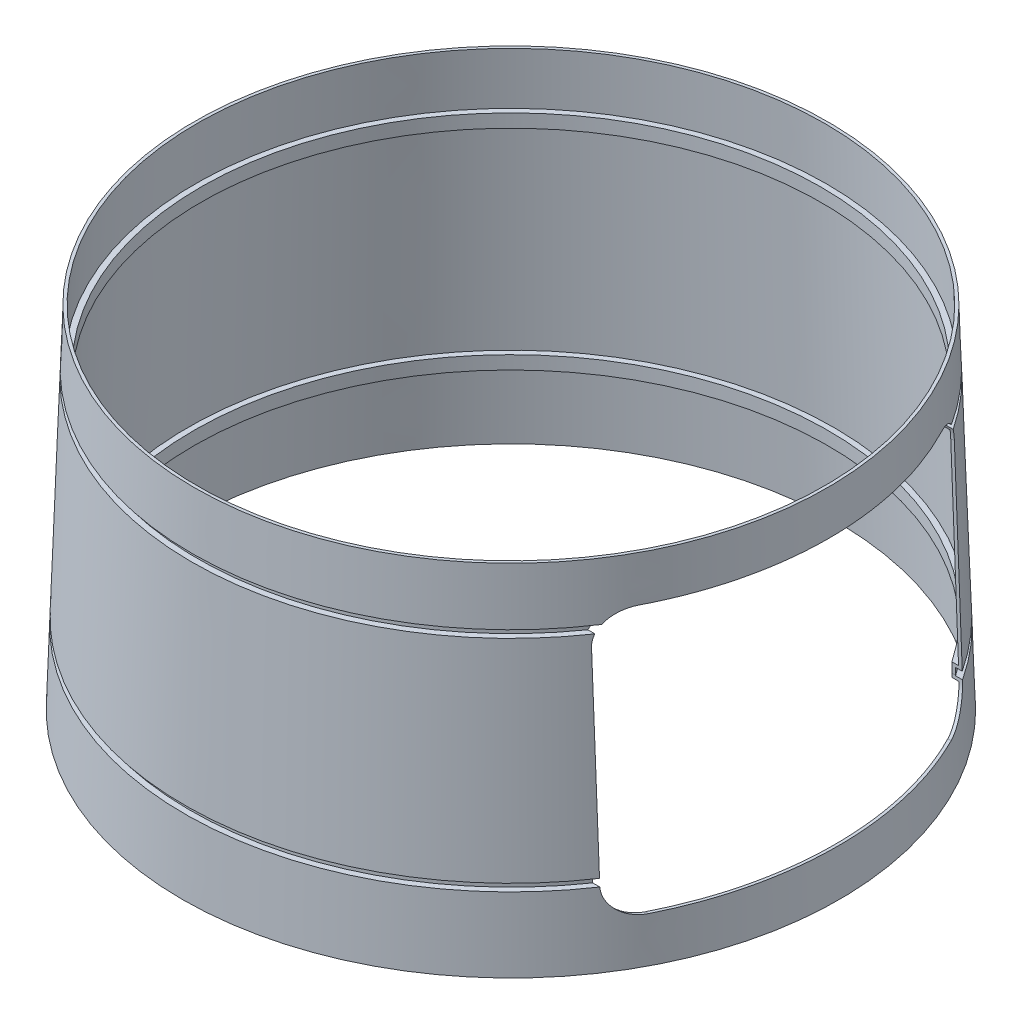
SolidWorks part; units mm, degrees
ref_plane "Front" through (0, 0, 0) normal (0, 0, 1) x (1, 0, 0)
ref_plane "Top" through (0, 0, 0) normal (0, 1, 0) x (1, 0, 0)
ref_plane "Right" through (0, 0, 0) normal (1, 0, 0) x (0, 0, -1)
sketch "Sketch1" plane through (0, 0, 0) normal (0, 0, 1) x (1, 0, 0)
  line L0 (0, 0) -> (109.9792, 0)
  line L1 (109.9792, 0) -> (109.1612, 24.3759)
  line L2 (106.0385, 117.4292) -> (0, 117.4292)
  line L3 (0, 117.4292) -> (0, 0)
  line L4 (106.6704, 98.5997) -> (104.8, 98.5997)
  line L5 (104.8, 98.5997) -> (104.8, 96.1587)
  line L6 (104.8, 96.1587) -> (106.7523, 96.1587)
  line L7 (109.0793, 26.8169) -> (107.2089, 26.8169)
  line L8 (107.2089, 26.8169) -> (107.2089, 24.3759)
  line L9 (107.2089, 24.3759) -> (109.1612, 24.3759)
  line L10 (106.6704, 98.5997) -> (106.0385, 117.4292)
  line L11 (109.0793, 26.8169) -> (106.7523, 96.1587)
  line L12 (109.9792, 0) -> (-109.9792, 0) construction
  dimension "D1" = 88.078
revolve "Revolve1" add sketch "Sketch1" angle 360 about L3
shell "Shell1" thickness 1
ref_plane "Plane1" through (109.8555, 3.6865, 0) normal (0.9994, 0.0335, 0) x (0, 0, -1)
sketch "Sketch2" plane through (109.8555, 3.6865, 0) normal (0.9994, 0.0335, 0) x (0, 0, -1)
  line L1 (-50.8692, 11.5651) -> (49.8692, 11.5651)
  line L2 (-60.8692, 21.5651) -> (-60.8692, 89.3601)
  line L3 (-50.8692, 99.3601) -> (49.8692, 99.3601)
  line L4 (59.8692, 21.5651) -> (59.8692, 89.3601)
  line L5 (-60.8692, 11.5651) -> (59.8692, 99.3601) construction
  line L6 (-60.8692, 99.3601) -> (59.8692, 11.5651) construction
  line L12 (54.3692, 99.3601) -> (-54.3692, 99.3601) construction
  line L13 (59.8692, 8.2741) -> (59.8692, 93.8632) construction
  arc A0 (49.8692, 99.3601) -> (59.8692, 89.3601) centre (49.8692, 89.3601) cw
  arc A1 (-50.8692, 11.5651) -> (-60.8692, 21.5651) centre (-50.8692, 21.5651) cw
  arc A2 (49.8692, 11.5651) -> (59.8692, 21.5651) centre (49.8692, 21.5651) ccw
  arc A3 (-60.8692, 89.3601) -> (-50.8692, 99.3601) centre (-50.8692, 89.3601) cw
  point P0 (-0.5, 55.4626)
  dimension "D1" = 10
extrude "Cut-Extrude1" cut sketch "Sketch2" against normal up to next
